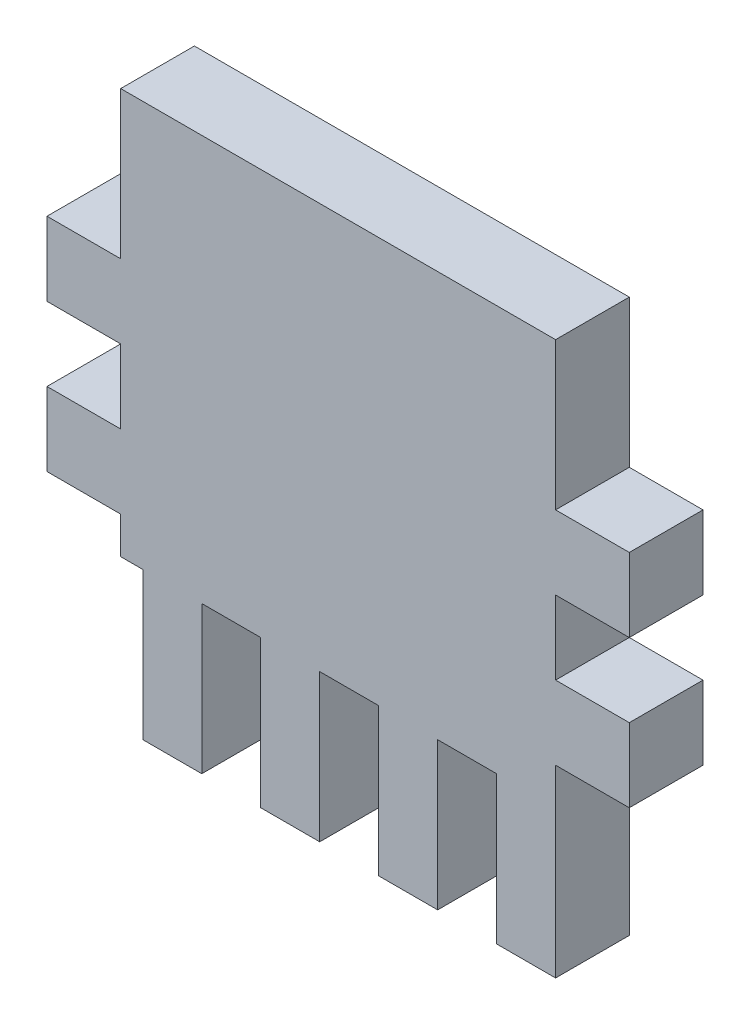
SolidWorks part; units mm, degrees
ref_plane "Plan de face" through (0, 0, 0) normal (0, 0, 1) x (1, 0, 0)
ref_plane "Plan de dessus" through (0, 0, 0) normal (0, 1, 0) x (1, 0, 0)
ref_plane "Plan de droite" through (0, 0, 0) normal (1, 0, 0) x (0, 0, -1)
sketch "Esquisse2" plane through (0, 0, 0) normal (0, 0, 1) x (1, 0, 0)
  line L0 (27.5058, -4) -> (27.5058, 16) construction
  line L1 (-13.9093, -8.7131) -> (15.5907, -8.7131)
  line L2 (-13.9093, -8.7131) -> (-13.9093, 18.7869)
  line L3 (-13.9093, 18.7869) -> (15.5907, 18.7869)
  line L4 (15.5907, -8.7131) -> (15.5907, 18.7869)
  line L5 (27.5058, 16) -> (-10.8221, 16) construction
  line L6 (-18.9093, -6.2131) -> (-13.9093, -6.2131)
  line L7 (-12.4093, -8.7131) -> (-8.4093, -8.7131)
  line L8 (-12.4093, -8.7131) -> (-12.4093, -18.7131)
  line L9 (-12.4093, -18.7131) -> (-8.4093, -18.7131)
  line L10 (-8.4093, -8.7131) -> (-8.4093, -18.7131)
  line L11 (-4.4093, -8.7131) -> (-0.4093, -8.7131)
  line L12 (-4.4093, -8.7131) -> (-4.4093, -18.7131)
  line L13 (-4.4093, -18.7131) -> (-0.4093, -18.7131)
  line L14 (-0.4093, -8.7131) -> (-0.4093, -18.7131)
  line L15 (20.5907, -6.2131) -> (15.5907, -6.2131)
  line L16 (15.5907, -8.7131) -> (15.5907, -1.2131)
  line L17 (15.5907, -1.2131) -> (20.5907, -1.2131)
  line L18 (20.5907, -6.2131) -> (20.5907, -1.2131)
  line L19 (15.5907, 3.7869) -> (20.5907, 3.7869)
  line L20 (15.5907, 3.7869) -> (15.5907, 8.7869)
  line L21 (15.5907, 8.7869) -> (20.5907, 8.7869)
  line L22 (20.5907, 3.7869) -> (20.5907, 8.7869)
  line L24 (-13.9093, -8.7131) -> (-13.9093, -1.2131)
  line L25 (-13.9093, -1.2131) -> (-18.9093, -1.2131)
  line L26 (-18.9093, -6.2131) -> (-18.9093, -1.2131)
  line L27 (3.5907, -8.7131) -> (7.5907, -8.7131)
  line L28 (3.5907, -8.7131) -> (3.5907, -18.7131)
  line L29 (3.5907, -18.7131) -> (7.5907, -18.7131)
  line L30 (7.5907, -8.7131) -> (7.5907, -18.7131)
  line L31 (15.5907, -8.7131) -> (11.5907, -8.7131)
  line L32 (15.5907, -8.7131) -> (15.5907, -18.7131)
  line L33 (15.5907, -18.7131) -> (11.5907, -18.7131)
  line L34 (11.5907, -8.7131) -> (11.5907, -18.7131)
  line L35 (-13.9093, 3.7869) -> (-18.9093, 3.7869)
  line L36 (-13.9093, 3.7869) -> (-13.9093, 8.7869)
  line L37 (-13.9093, 8.7869) -> (-18.9093, 8.7869)
  line L38 (-18.9093, 3.7869) -> (-18.9093, 8.7869)
  dimension "D1" = 29.5
  dimension "D2" = 27.5
  dimension "D3" = 20
  dimension "D4" = 5
  dimension "D5" = 5
  dimension "D6" = 5
  dimension "D7" = 10
  dimension "D8" = 10
  dimension "D9" = 5
  dimension "D10" = 10
  dimension "D11" = 4
  dimension "D12" = 10
  dimension "D13" = 4
  dimension "D14" = 4
  dimension "D15" = 10
  dimension "D16" = 90
  dimension "D17" = 4
  dimension "D18" = 4
  dimension "D19" = 5
  dimension "D20" = 5
  dimension "D21" = 5
  dimension "D22" = 5
  dimension "D23" = 4
  dimension "D24" = 4
  dimension "D25" = 10
  dimension "D26" = 5
  dimension "D27" = 5
extrude "Boss.-Extru.1" add sketch "Esquisse2" along normal blind 5 contours L10 L1 L8 L9 | L14 L1 L12 L13 | L30 L1 L28 L29 | L1 L34 L33 L32 | L15 L18 L17 L4 | L19 L22 L21 L4 | L26 L6 L2 L25 | L1 L4 L3 L2 | L38 L37 L36 L35
